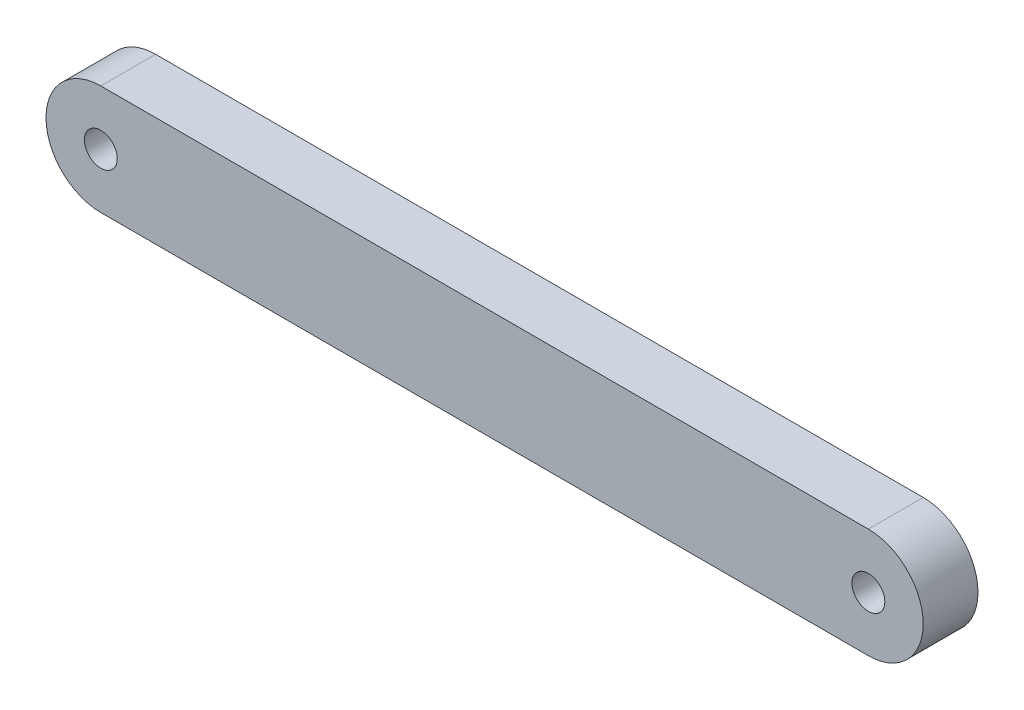
SolidWorks part; units mm, degrees
ref_plane "Piano frontale" through (0, 0, 0) normal (0, 0, 1) x (1, 0, 0)
ref_plane "Piano superiore" through (0, 0, 0) normal (0, 1, 0) x (1, 0, 0)
ref_plane "Piano destro" through (0, 0, 0) normal (1, 0, 0) x (0, 0, -1)
sketch "Sketch1" plane through (0, 0, 0) normal (0, 0, 1) x (1, 0, 0)
  line L0 (-350, 0) -> (350, 0) construction
  line L1 (-350, 50) -> (350, 50)
  line L2 (-350, -50) -> (350, -50)
  arc A0 (-350, 50) -> (-350, -50) centre (-350, 0) ccw
  arc A1 (350, -50) -> (350, 50) centre (350, 0) ccw
  point P3 (0, 0)
  dimension "D1" = 700
  dimension "D2" = 100
extrude "Boss-Extrude1" add sketch "Sketch1" along normal mid plane 50
sketch "Sketch2" plane through (0, 0, 25) normal (0, 0, 1) x (1, 0, 0)
  circle A0 centre (-350, 0) radius 15
  circle A1 centre (350, 0) radius 15
  dimension "D1" = 30
extrude "Cut-Extrude1" cut sketch "Sketch2" against normal through all
